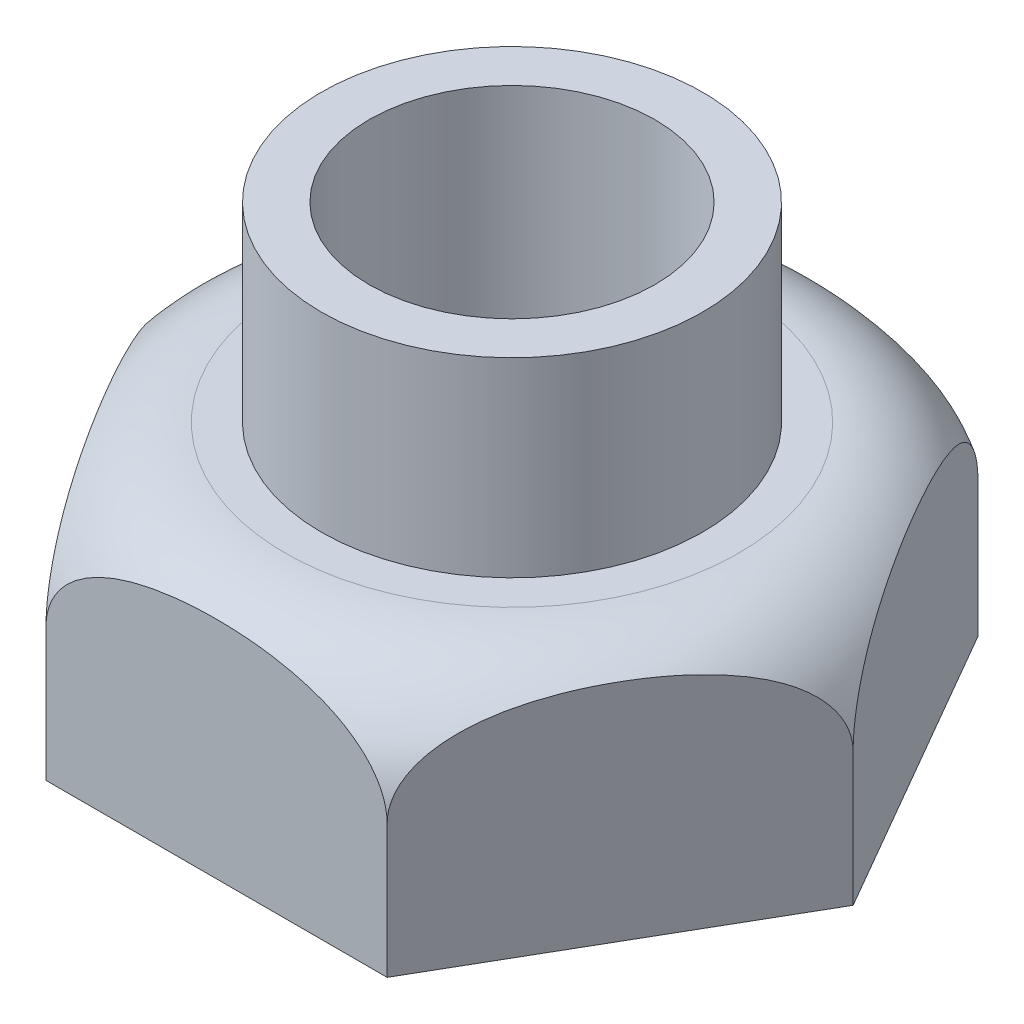
SolidWorks part; units mm, degrees
ref_plane "Front Plane" through (0, 0, 0) normal (0, 0, 1) x (1, 0, 0)
ref_plane "Top Plane" through (0, 0, 0) normal (0, 1, 0) x (1, 0, 0)
ref_plane "Right Plane" through (0, 0, 0) normal (1, 0, 0) x (0, 0, -1)
sketch "Sketch1" plane through (0, 0, 0) normal (0, 1, 0) x (1, 0, 0)
  line L1 (89.4893, 0) -> (44.7446, 77.5)
  line L2 (44.7446, 77.5) -> (-44.7446, 77.5)
  line L3 (-44.7446, 77.5) -> (-89.4893, 0)
  line L4 (-89.4893, 0) -> (-44.7446, -77.5)
  line L5 (-44.7446, -77.5) -> (44.7446, -77.5)
  line L6 (44.7446, -77.5) -> (89.4893, 0)
  circle A0 centre (0, 0) radius 77.5 construction
  dimension "D1" = 155
extrude "Boss-Extrude1" add sketch "Sketch1" along normal blind 65
sketch "Sketch4" plane through (0, 0, 0) normal (0, 1, 0) x (1, 0, 0)
  circle A0 centre (0, 0) radius 50
  dimension "D1" = 100
extrude "Boss-Extrude3" add sketch "Sketch4" along normal blind 50 from surface at 65 starting at face at (0, 65, 0)
sketch "Sketch6" plane through (0, 0, 0) normal (0, 1, 0) x (1, 0, 0)
  circle A0 centre (0, 0) radius 37.5
  dimension "D1" = 75
extrude "Cut-Extrude1" cut sketch "Sketch6" along normal through all both and the other way through all
sketch "Sketch7" plane through (0, 0, 0) normal (0, 0, 1) x (1, 0, 0)
  line L0 (89.4893, 65) -> (89.4893, 0) construction
  line L1 (44.7446, 65) -> (89.4893, 65) construction
  line L2 (89.4893, 35) -> (89.4893, 65)
  line L3 (89.4893, 65) -> (59.4893, 65)
  line L4 (0, 0) -> (0, 17.7145) construction
  arc A0 (89.4893, 35) -> (59.4893, 65) centre (59.4893, 35) ccw
  dimension "D1" = 30
revolve "Cut-Revolve1" cut sketch "Sketch7" angle 360 about L4
